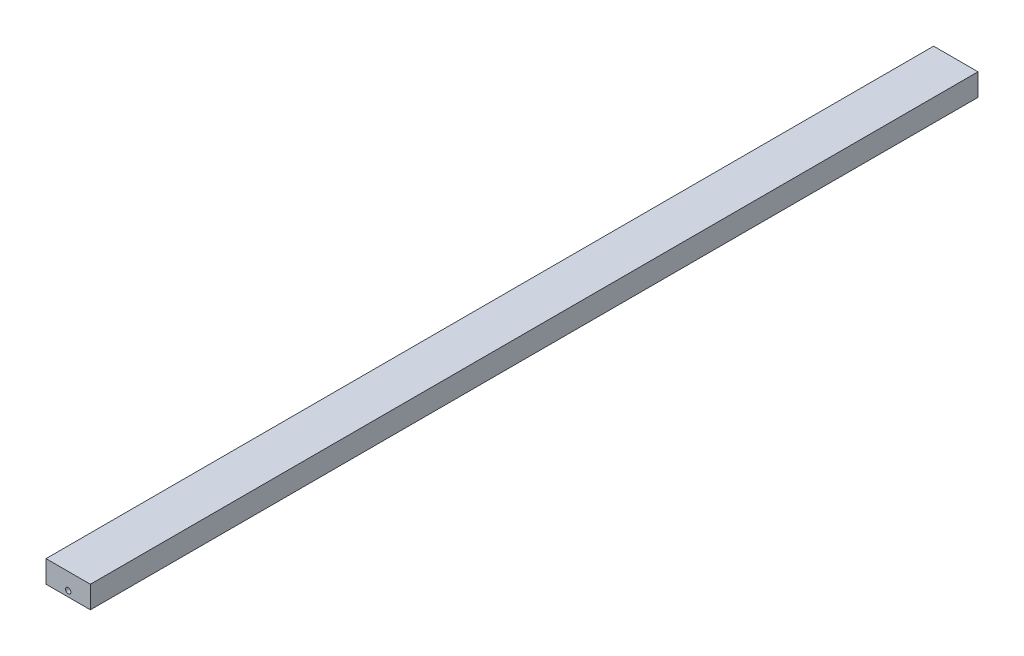
SolidWorks part; units mm, degrees
ref_plane "Ebene vorne" through (0, 0, 0) normal (0, 0, 1) x (1, 0, 0)
ref_plane "Ebene oben" through (0, 0, 0) normal (0, 1, 0) x (1, 0, 0)
ref_plane "Ebene rechts" through (0, 0, 0) normal (1, 0, 0) x (0, 0, -1)
sketch "Skizze1" plane through (0, 0, 0) normal (0, 0, 1) x (1, 0, 0)
  line L1 (-5, 2.5) -> (5, 2.5)
  line L2 (-5, 2.5) -> (-5, -2.5)
  line L3 (-5, -2.5) -> (5, -2.5)
  line L4 (5, 2.5) -> (5, -2.5)
  line L5 (-5, 2.5) -> (5, -2.5) construction
  line L6 (-5, -2.5) -> (5, 2.5) construction
  point P0 (0, 0)
  dimension "D1" = 10
  dimension "D2" = 5
extrude "Aufsatz-Linear austragen1" add sketch "Skizze1" along normal blind 200
sketch "Skizze2" plane through (0, 0, 0) normal (0, 0, 1) x (1, 0, 0)
  line L0 (0, -2.75) -> (0, 2.75) construction
  circle A0 centre (0, -1.25) radius 0.6
  point P2 (0, 0)
  dimension "D1" = 1.2
  dimension "D2" = 1.25
extrude "Schnitt-Linear austragen1" cut sketch "Skizze2" along normal through all
